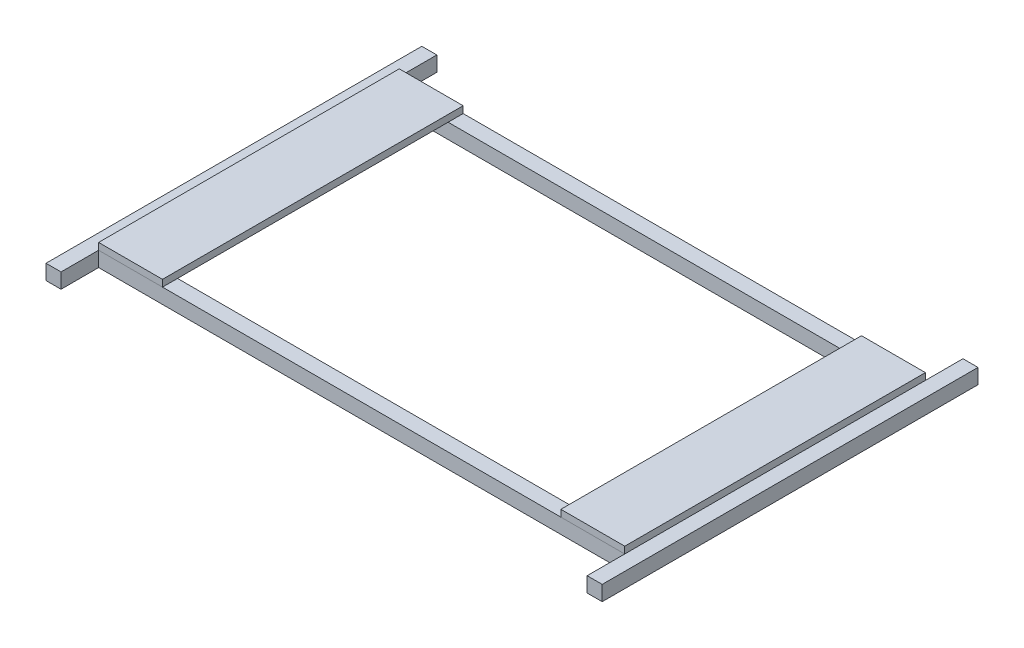
SolidWorks part; units mm, degrees
ref_plane "Front Plane" through (0, 0, 0) normal (0, 0, 1) x (1, 0, 0)
ref_plane "Top Plane" through (0, 0, 0) normal (0, 1, 0) x (1, 0, 0)
ref_plane "Right Plane" through (0, 0, 0) normal (1, 0, 0) x (0, 0, -1)
sketch "Sketch1" plane through (0, 0, 0) normal (0, 1, 0) x (1, 0, 0)
  line L0 (365.2727, -39.6794) -> (365.2727, 10.3206)
  line L1 (-334.7273, 390.3206) -> (365.2727, 390.3206)
  line L2 (-334.7273, 390.3206) -> (-334.7273, 30.3206)
  line L3 (-334.7273, 30.3206) -> (365.2727, 30.3206)
  line L4 (365.2727, 390.3206) -> (365.2727, 30.3206)
  line L5 (-354.7273, 10.3206) -> (-334.7273, 10.3206)
  line L6 (-334.7273, 390.3206) -> (-354.7273, 390.3206)
  line L7 (-334.7273, 10.3206) -> (365.2727, 10.3206)
  line L8 (-354.7273, 10.3206) -> (-354.7273, 225.7942)
  line L9 (-334.7273, 410.3206) -> (365.2727, 410.3206)
  line L10 (385.2727, 10.3206) -> (385.2727, 410.3206)
  line L11 (365.2727, 410.3206) -> (385.2727, 410.3206)
  line L12 (365.2727, 390.3206) -> (385.2727, 390.3206)
  line L13 (365.2727, 460.3206) -> (385.2727, 460.3206)
  line L14 (385.2727, 460.3206) -> (385.2727, 410.3206)
  line L15 (365.2727, 10.3206) -> (365.2727, 30.3206)
  line L16 (365.2727, -39.6794) -> (385.2727, -39.6794)
  line L17 (385.2727, -39.6794) -> (385.2727, 10.3206)
  line L18 (365.2727, 460.3206) -> (365.2727, 410.3206)
  line L19 (-334.7273, -39.6794) -> (-354.7273, -39.6794)
  line L20 (-354.7273, -39.6794) -> (-354.7273, 10.3206)
  line L21 (-354.7273, 225.7942) -> (-354.7273, 460.3206)
  line L22 (-354.7273, 460.3206) -> (-334.7273, 460.3206)
  line L23 (365.2727, 410.3206) -> (365.2727, 390.3206)
  line L24 (-334.7273, 460.3206) -> (-334.7273, 410.3206)
  line L25 (-334.7273, 410.3206) -> (-334.7273, 390.3206)
  line L26 (-334.7273, 30.3206) -> (-334.7273, 10.3206)
  line L27 (-334.7273, 10.3206) -> (-334.7273, -39.6794)
  line L28 (365.2727, 30.3206) -> (385.2727, 30.3206)
  line L29 (365.2727, 10.3206) -> (385.2727, 10.3206)
  line L30 (-334.7273, 30.3206) -> (-354.7273, 30.3206)
  line L31 (-334.7273, 410.3206) -> (-354.7273, 410.3206)
  point P0 (0, 0)
  point P15 (375.2727, 460.3206)
  point P22 (0, 0)
  dimension "D1" = 20
  dimension "D2" = 20
  dimension "D3" = 500
  dimension "D4" = 50
  dimension "D5" = 70
  dimension "D6" = 70
  dimension "D7" = 70
  dimension "D8" = 20
  dimension "D9" = 700
  dimension "D10" = 20
extrude "Boss-Extrude1" add sketch "Sketch1" against normal blind 20 contours L9 L25 L1 L23 | L30 L2 L6 L21 L8 | L27 L5 L20 L19 | L26 L30 L8 L5 | L3 L26 L7 L15 | L29 L0 L16 L17 | L15 L29 L10 L28 | L4 L28 L10 L12 | L11 L23 L12 L10 | L13 L18 L11 L14 | L31 L24 L22 L21 | L25 L31 L21 L6
sketch "Sketch3" plane through (0, 0, 0) normal (0, 1, 0) x (1, 0, 0)
  line L0 (-334.7273, 10.3206) -> (365.2727, 10.3206) construction
  line L1 (-334.7273, 410.3206) -> (-249.7273, 410.3206)
  line L2 (-334.7273, 410.3206) -> (-334.7273, 10.3206)
  line L3 (-334.7273, 10.3206) -> (-249.7273, 10.3206)
  line L4 (-249.7273, 410.3206) -> (-249.7273, 10.3206)
  line L6 (365.2727, 410.3206) -> (280.2727, 410.3206)
  line L7 (365.2727, 410.3206) -> (365.2727, 10.3206)
  line L8 (365.2727, 10.3206) -> (280.2727, 10.3206)
  line L9 (280.2727, 410.3206) -> (280.2727, 10.3206)
  dimension "D1" = 85
  dimension "D2" = 85
extrude "Boss-Extrude5" add sketch "Sketch3" along normal blind 9 separate body
